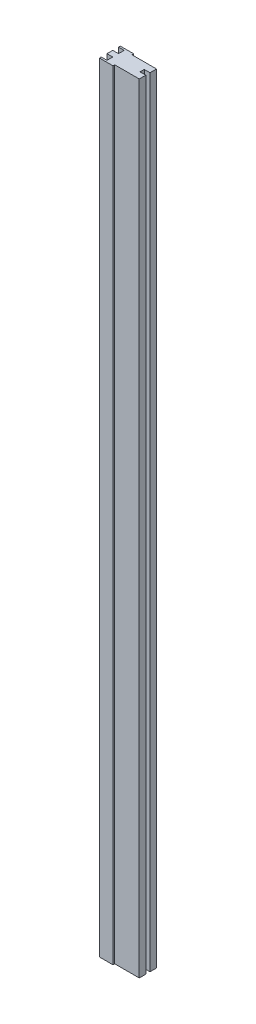
SolidWorks part; units mm, degrees
ref_plane "Спереди" through (0, 0, 0) normal (0, 0, 1) x (1, 0, 0)
ref_plane "Сверху" through (0, 0, 0) normal (0, 1, 0) x (1, 0, 0)
ref_plane "Справа" through (0, 0, 0) normal (1, 0, 0) x (0, 0, -1)
sketch "Эскиз1" plane through (0, 0, 0) normal (0, 1, 0) x (1, 0, 0)
  line L4 (-10, -14.9403) -> (-10, -5)
  line L5 (-10, -5) -> (-20, -5)
  line L6 (-20, -5) -> (-20, 0)
  line L7 (-32.4821, 0) -> (46.2952, 0) construction
  line L13 (46, -15) -> (46, -3.6855)
  line L14 (46, -3.6855) -> (36, -3.6855)
  line L15 (36, -3.6855) -> (36, 3.6855)
  line L17 (-10, -14.9403) -> (-20, -14.9403)
  line L18 (-20, -14.9403) -> (-20, -18)
  line L19 (-20, -18) -> (3.3428, -18)
  line L20 (3.3428, -18) -> (3.3428, -15)
  line L21 (3.3428, -15) -> (46, -15)
  line L22 (3.3428, 15) -> (46, 15)
  line L23 (3.3428, 18) -> (3.3428, 15)
  line L24 (-20, 18) -> (3.3428, 18)
  line L25 (-20, 14.9403) -> (-20, 18)
  line L26 (-10, 14.9403) -> (-20, 14.9403)
  line L27 (46, 3.6855) -> (36, 3.6855)
  line L28 (46, 15) -> (46, 3.6855)
  line L30 (-20, 5) -> (-20, 0)
  line L31 (-10, 5) -> (-20, 5)
  line L32 (-10, 14.9403) -> (-10, 5)
  point P21 (0, 0)
  point P26 (0, 0)
  dimension "D1" = 66
  dimension "D2" = 30
extrude "Бобышка-Вытянуть1" add sketch "Эскиз1" along normal blind 1350
